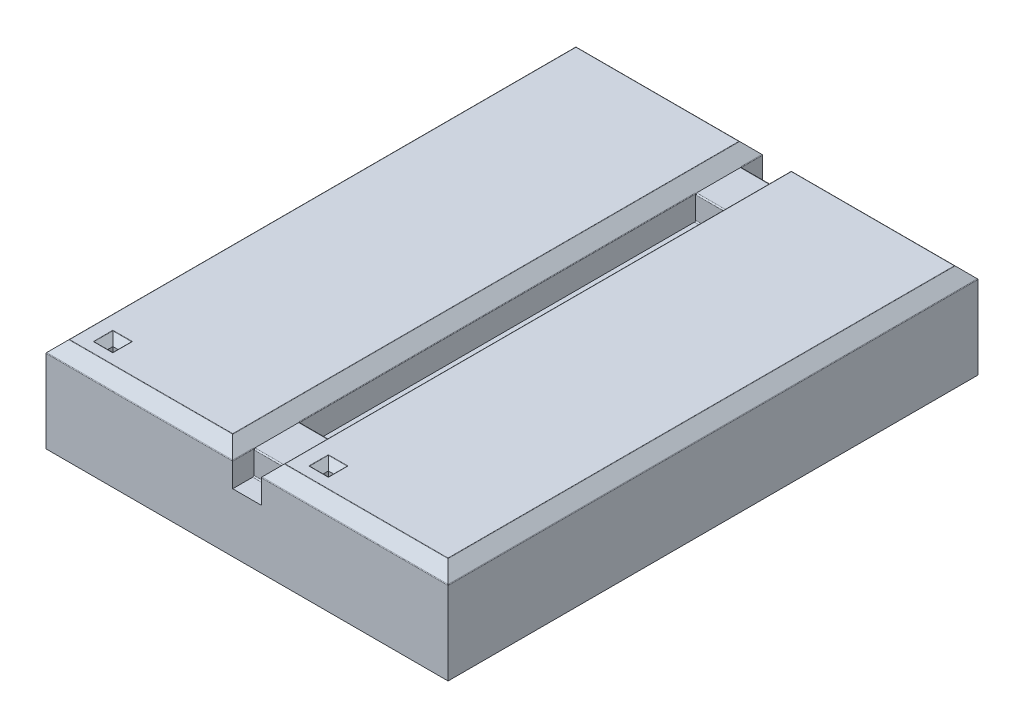
SolidWorks part; units mm, degrees
material "ABS"
ref_plane "Front Plane" through (0, 0, 0) normal (0, 0, 1) x (1, 0, 0)
ref_plane "Top Plane" through (0, 0, 0) normal (0, 1, 0) x (1, 0, 0)
ref_plane "Right Plane" through (0, 0, 0) normal (1, 0, 0) x (0, 0, -1)
sketch "Sketch1" plane through (0, 0, 0) normal (0, 1, 0) x (1, 0, 0)
  line L1 (-17.3, 22.8) -> (17.3, 22.8)
  line L2 (-17.3, 22.8) -> (-17.3, -22.8)
  line L3 (-17.3, -22.8) -> (17.3, -22.8)
  line L4 (17.3, 22.8) -> (17.3, -22.8)
  line L5 (-17.3, 22.8) -> (17.3, -22.8) construction
  line L6 (-17.3, -22.8) -> (17.3, 22.8) construction
  point P0 (0, 0)
  dimension "D1" = 34.6
  dimension "D2" = 45.6
extrude "Boss-Extrude1" add sketch "Sketch1" along normal blind 8.15
sketch "Sketch2" plane through (0, 8.15, 0) normal (0, 1, 0) x (1, 0, 0)
  line L0 (0, 22.8) -> (0, -22.8) construction
  line L1 (17.3, 22.8) -> (-17.3, 22.8) construction
  line L2 (-17.3, -22.8) -> (17.3, -22.8) construction
  line L4 (-1.235, -22.8) -> (1.235, -22.8)
  line L5 (-1.235, -22.8) -> (-1.235, 22.8)
  line L6 (-1.235, 22.8) -> (1.235, 22.8)
  line L7 (1.235, -22.8) -> (1.235, 22.8)
  line L8 (-1.235, -22.8) -> (1.235, 22.8) construction
  line L9 (-1.235, 22.8) -> (1.235, -22.8) construction
  point P6 (0, 0)
  dimension "D1" = 2.47
extrude "Cut-Extrude1" cut sketch "Sketch2" against normal blind 3.09
chamfer "Chamfer1" distance 1 angle 45 8 edges at (9.2675, 8.15, -22.8) (17.3, 8.15, 0) (9.2675, 8.15, 22.8) (1.235, 8.15, 0) (-9.2675, 8.15, 22.8) (-17.3, 8.15, 0) (-9.2675, 8.15, -22.8) (-1.235, 8.15, 0)
sketch "Sketch3" plane through (0, 5.06, 0) normal (0, 1, 0) x (1, 0, 0)
  line L0 (1.235, -22.8) -> (1.235, 22.8) construction
  line L1 (-1.235, 20.98) -> (1.235, 20.98)
  line L2 (-1.235, 20.98) -> (-1.235, 17.03)
  line L3 (-1.235, 17.03) -> (1.235, 17.03)
  line L4 (1.235, 20.98) -> (1.235, 17.03)
  line L5 (-1.235, 20.98) -> (1.235, 17.03) construction
  line L6 (-1.235, 17.03) -> (1.235, 20.98) construction
  line L7 (-1.235, -22.8) -> (1.235, -22.8) construction
  line L8 (-1.235, -17.03) -> (1.235, -17.03)
  line L9 (-1.235, -17.03) -> (-1.235, -20.98)
  line L10 (-1.235, -20.98) -> (1.235, -20.98)
  line L11 (1.235, -17.03) -> (1.235, -20.98)
  line L12 (-1.235, -17.03) -> (1.235, -20.98) construction
  line L13 (-1.235, -20.98) -> (1.235, -17.03) construction
  line L14 (1.235, 22.8) -> (-1.235, 22.8) construction
  point P0 (0, 19.005)
  point P7 (0, -19.005)
  dimension "D1" = 3.95
  dimension "D2" = 3.95
  dimension "D3" = 1.82
  dimension "D4" = 1.82
extrude "Boss-Extrude2" add sketch "Sketch3" along normal up to vertex (2.09 mm away)
sketch "Sketch4" plane through (0, 8.15, 0) normal (0, 1, 0) x (1, 0, 0)
  line L0 (-1.235, -22.8) -> (-17.3, -22.8) construction
  line L1 (-14.5, -19.85) -> (-14.05, -19.85)
  line L2 (-14.5, -19.85) -> (-14.5, -20.3)
  line L3 (-14.5, -20.3) -> (-14.05, -20.3)
  line L4 (-14.05, -19.85) -> (-14.05, -20.3)
  line L5 (-14.5, -19.85) -> (-14.05, -20.3) construction
  line L6 (-14.5, -20.3) -> (-14.05, -19.85) construction
  line L671 (4.5, -19.85) -> (4.5, -20.3)
  line L672 (4.5, -19.85) -> (4.05, -19.85)
  line L673 (4.05, -19.85) -> (4.05, -20.3)
  line L674 (4.5, -20.3) -> (4.05, -20.3)
  point P0 (-14.275, -20.075)
  dimension "D1" = 0.45
  dimension "D3" = 2.5
  dimension "D6" = 17
extrude "Cut-Extrude2" cut sketch "Sketch4" against normal blind 7.09
chamfer "Chamfer2" distance 0.6 angle 45 8 edges at (-14.275, 8.15, 20.3) (-14.05, 8.15, 20.075) (-14.5, 8.15, 20.075) (-14.275, 8.15, 19.85) (4.275, 8.15, 20.3) (4.5, 8.15, 20.075) (4.05, 8.15, 20.075) (4.275, 8.15, 19.85)
pattern_linear "LPattern9" [suppressed] count 17 spacing 2.5
fillet "Fillet2" radius 0.05 16 edges at (-9.2675, 8.15, -21.8) (-2.235, 8.15, 0) (-9.2675, 8.15, 21.8) (-16.3, 8.15, 0) (-14.275, 8.15, 19.25) (-15.1, 8.15, 20.075) (-14.275, 8.15, 20.9) (-13.45, 8.15, 20.075) (9.2675, 8.15, 21.8) (2.235, 8.15, 0) (9.2675, 8.15, -21.8) (16.3, 8.15, 0) (4.275, 8.15, 19.25) (3.45, 8.15, 20.075) (4.275, 8.15, 20.9) (5.1, 8.15, 20.075)
fillet "Fillet3" radius 0.1 12 edges at (-9.2675, 7.15, -22.8) (9.2675, 7.15, -22.8) (-17.3, 7.15, 0) (-9.2675, 7.15, 22.8) (-1.235, 7.15, -21.89) (-1.235, 7.15, 21.89) (-1.235, 7.15, 0) (1.235, 7.15, -21.89) (1.235, 7.15, 0) (1.235, 7.15, 21.89) (9.2675, 7.15, 22.8) (17.3, 7.15, 0)
fillet "Fillet4" radius 0.1 8 edges at (0, 5.06, 20.98) (0, 7.15, 20.98) (0, 7.15, 17.03) (0, 5.06, 17.03) (0, 5.06, -17.03) (0, 7.15, -17.03) (0, 7.15, -20.98) (0, 5.06, -20.98)
